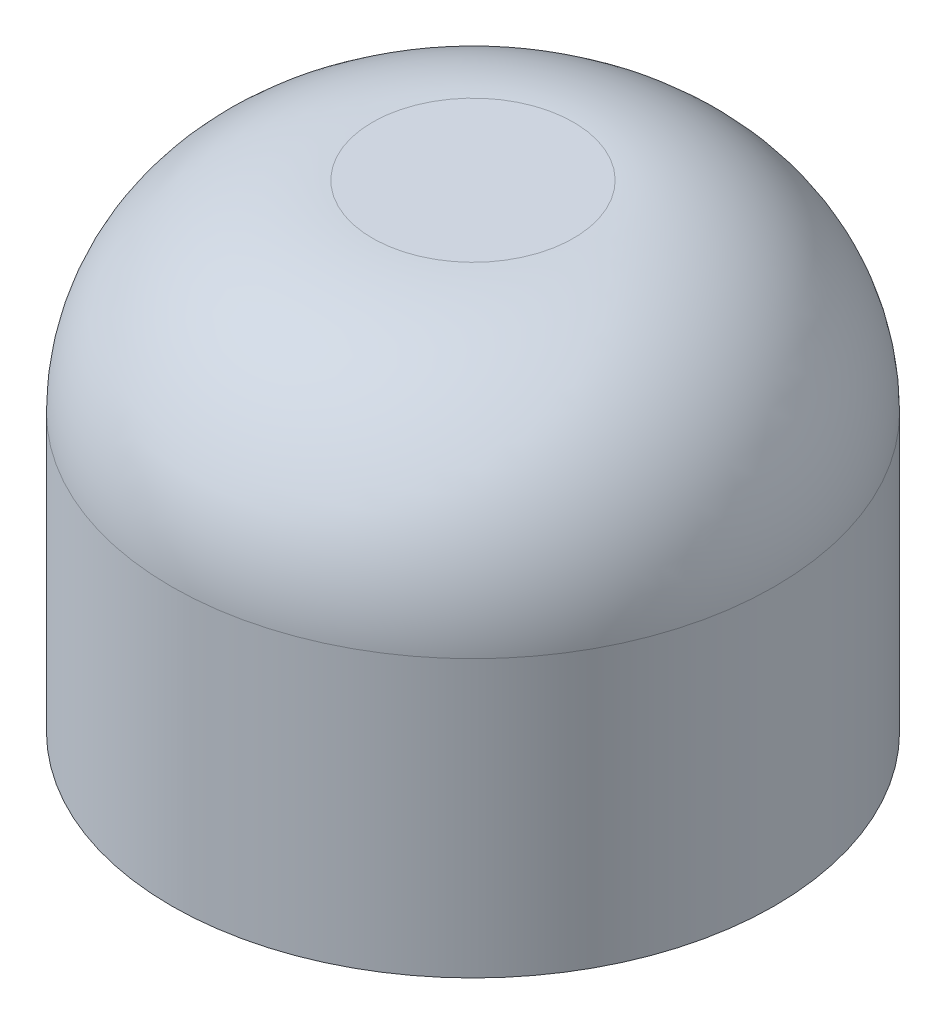
SolidWorks part; units mm, degrees
ref_plane "Piano frontale" through (0, 0, 0) normal (0, 0, 1) x (1, 0, 0)
ref_plane "Piano superiore" through (0, 0, 0) normal (0, 1, 0) x (1, 0, 0)
ref_plane "Piano destro" through (0, 0, 0) normal (1, 0, 0) x (0, 0, -1)
sketch "Schizzo1" plane through (0, 0, 0) normal (0, 0, 1) x (1, 0, 0)
  line L6 (0, 0) -> (1.5, 0)
  line L7 (1.5, 0) -> (1.5, -3)
  line L8 (1.5, -3) -> (3, -3)
  line L9 (3, -3) -> (3, -0.25)
  line L10 (1, 1.75) -> (0, 1.75)
  line L11 (0, 1.75) -> (0, 0)
  arc A0 (3, -0.25) -> (1, 1.75) centre (1, -0.25) ccw
  dimension "D5" = 2
  dimension "D1" = 1.5
  dimension "D2" = 1.5
  dimension "D3" = 3
  dimension "D4" = 1.75
revolve "Rivoluzione1" add sketch "Schizzo1" angle 360 about L11
